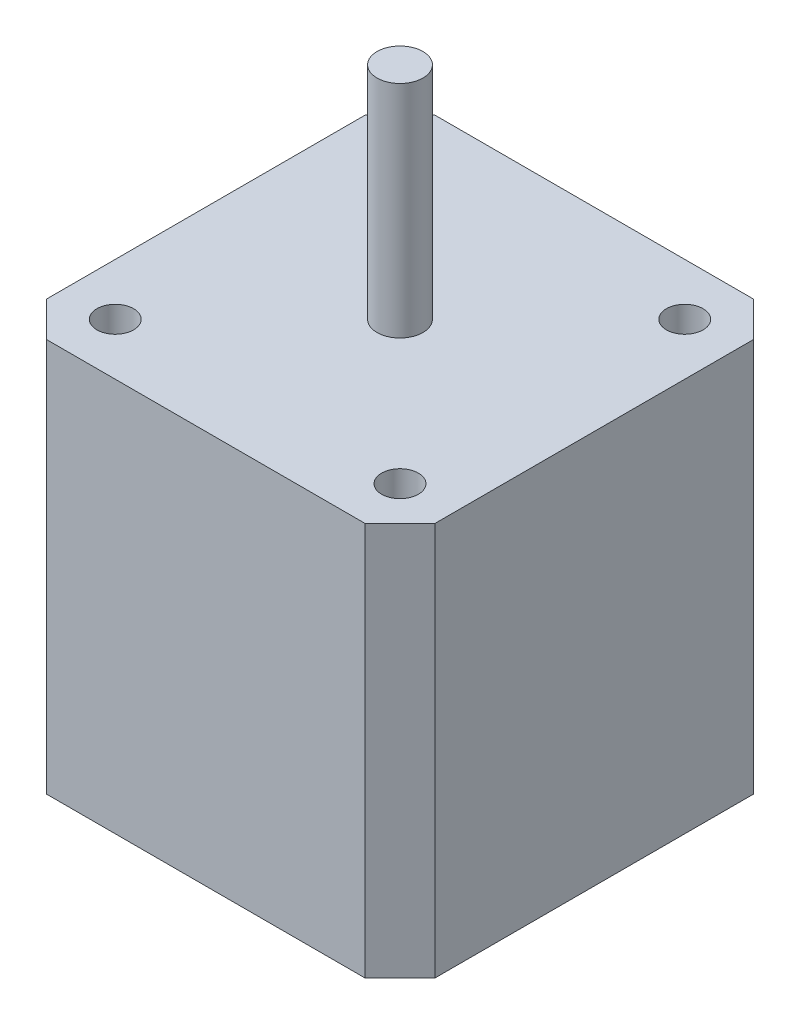
SolidWorks part; units mm, degrees
ref_plane "Front Plane" through (0, 0, 0) normal (0, 0, 1) x (1, 0, 0)
ref_plane "Top Plane" through (0, 0, 0) normal (0, 1, 0) x (1, 0, 0)
ref_plane "Right Plane" through (0, 0, 0) normal (1, 0, 0) x (0, 0, -1)
sketch "Sketch1" plane through (0, 0, 0) normal (0, 1, 0) x (1, 0, 0)
  line L1 (21.15, -21.15) -> (-21.15, -21.15)
  line L2 (21.15, -21.15) -> (21.15, 21.15)
  line L3 (21.15, 21.15) -> (-21.15, 21.15)
  line L4 (-21.15, -21.15) -> (-21.15, 21.15)
  line L5 (21.15, -21.15) -> (-21.15, 21.15) construction
  line L6 (21.15, 21.15) -> (-21.15, -21.15) construction
  point P0 (0, 0)
  dimension "D1" = 42.3
extrude "Boss-Extrude1" add sketch "Sketch1" along normal blind 42.8625
sketch "Sketch2" plane through (0, 42.8625, 0) normal (0, 1, 0) x (1, 0, 0)
  line L1 (15.5, -15.5) -> (-15.5, -15.5) construction
  line L2 (15.5, -15.5) -> (15.5, 15.5) construction
  line L3 (15.5, 15.5) -> (-15.5, 15.5) construction
  line L4 (-15.5, -15.5) -> (-15.5, 15.5) construction
  line L5 (15.5, -15.5) -> (-15.5, 15.5) construction
  line L6 (15.5, 15.5) -> (-15.5, -15.5) construction
  circle A0 centre (-15.5, -15.5) radius 2
  circle A1 centre (-15.5, 15.5) radius 2
  circle A2 centre (15.5, 15.5) radius 2
  circle A3 centre (15.5, -15.5) radius 2
  point P0 (0, 0)
  dimension "D2" = 4
  dimension "D1" = 31
extrude "Cut-Extrude1" cut sketch "Sketch2" against normal blind 6.35
chamfer "Chamfer1" distance 3.81 angle 45 4 edges at (-21.15, 21.4312, 21.15) (21.15, 21.4312, 21.15) (21.15, 21.4312, -21.15) (-21.15, 21.4312, -21.15)
sketch "Sketch3" plane through (0, 42.8625, 0) normal (0, 1, 0) x (1, 0, 0)
  circle A0 centre (0, 0) radius 2.5
  dimension "D1" = 5
extrude "Boss-Extrude2" add sketch "Sketch3" along normal blind 24
equation "\"holder_width\"= 42mm"
equation "\"stepper_size\"= 42.3mm"
equation "\"D1@Sketch1\"=\"stepper_size\""
equation "\"stepper_hole_spacing\"= 31mm"
equation "\"D1@Sketch2\"=\"stepper_hole_spacing\""
